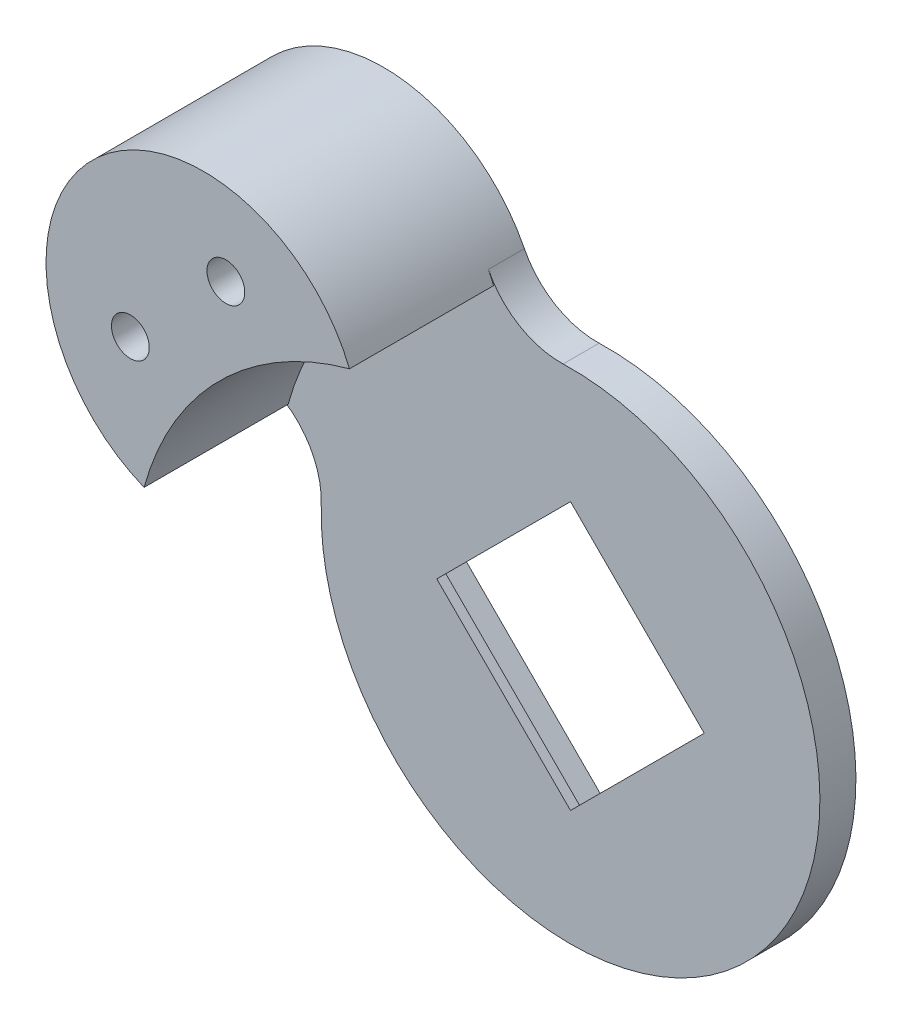
SolidWorks part; units mm, degrees
ref_plane "Front Plane" through (0, 0, 0) normal (0, 0, 1) x (1, 0, 0)
ref_plane "Top Plane" through (0, 0, 0) normal (0, 1, 0) x (1, 0, 0)
ref_plane "Right Plane" through (0, 0, 0) normal (1, 0, 0) x (0, 0, -1)
sketch "Sketch1" plane through (0, 0, 0) normal (0, 0, 1) x (1, 0, 0)
  arc A0 (-15.8844, 7.1509) -> (-38.6968, -15.6616) centre (-32.0888, 0.5429) ccw
  arc A2 (-19.7145, 12.9172) -> (-47.5228, -7.706) centre (-32.0888, 0.5429) ccw construction
  arc A3 (-15.8844, 7.1509) -> (-38.6968, -15.6616) centre (-7.3401, -24.2059) ccw
  dimension "D1" = 65
extrude "Boss-Extrude1" add sketch "Sketch1" along normal blind 16
sketch "Sketch2" plane through (0, 0, 0) normal (0, 0, -1) x (-1, 0, 0)
  circle A0 centre (7.3401, -24.2059) radius 27.6962 construction
  circle A1 centre (7.3401, -24.2059) radius 27.6962
  arc A2 (8.1602, 3.4781) -> (35.0241, -23.3857) centre (7.3401, -24.2059) ccw
  arc A3 (35.0241, -23.3857) -> (39.968, -15.083) centre (44.0202, -23.1192) cw
  arc A4 (38.6968, -15.6616) -> (15.8844, 7.1509) centre (7.3401, -24.2059) ccw
  arc A5 (38.6968, -15.6616) -> (15.8844, 7.1509) centre (32.0888, 0.5429) ccw
  arc A7 (39.968, -15.083) -> (16.4629, 8.4221) centre (32.0888, 0.5429) ccw
  arc A8 (8.1602, 3.4781) -> (16.4629, 8.4221) centre (8.4268, 12.4742) ccw
  point P0 (-30.618, 24.4257)
  point P13 (34.041, -16.8479)
  dimension "D3" = 9
  dimension "D1" = 0
  dimension "D2" = 0
extrude "Boss-Extrude2" add sketch "Sketch2" along normal blind 4
sketch "Sketch3" plane through (0, 0, -4) normal (0, 0, -1) x (-1, 0, 0)
  line L0 (40.2206, -1.932) -> (29.614, 8.6746) construction
  line L1 (7.3401, -24.2059) -> (34.9173, 3.3713) construction
  circle A0 centre (40.2206, -1.932) radius 2.1
  circle A1 centre (29.614, 8.6746) radius 2.1
  arc A2 (39.968, -15.083) -> (16.4629, 8.4221) centre (32.0888, 0.5429) ccw construction
  point P4 (44.4632, 12.9172)
  point P5 (-28.1337, 43.4891)
  dimension "D1" = 4.2
  dimension "D2" = 15
  dimension "D3" = 4
extrude "Cut-Extrude1" cut sketch "Sketch3" against normal through all
sketch "Sketch4" plane through (0, 0, -4) normal (0, 0, -1) x (-1, 0, 0)
  circle A0 centre (40.2206, -1.932) radius 4
  circle A1 centre (29.614, 8.6746) radius 4
  point P6 (-37.8732, 47.1192)
  point P7 (0, 0)
  point P8 (0, 0)
  dimension "D1" = 8
extrude "Cut-Extrude2" cut sketch "Sketch4" against normal offset from surface (14 mm away) 6 up to face at (-42.3206, -1.932, 16)
sketch "Sketch5" plane through (0, 0, -4) normal (0, 0, -1) x (-1, 0, 0)
  line L0 (23.6035, -24.2059) -> (7.3401, -7.9424)
  line L1 (23.6035, -24.2059) -> (7.3401, -40.4693)
  line L2 (7.3401, -7.9424) -> (-8.9234, -24.2059)
  line L3 (7.3401, -40.4693) -> (-8.9234, -24.2059)
  line L4 (23.6035, -24.2059) -> (-8.9234, -24.2059) construction
  line L5 (7.3401, -7.9424) -> (7.3401, -40.4693) construction
  line L6 (29.614, 8.6746) -> (40.2206, -1.932) construction
  arc A0 (8.1602, 3.4781) -> (35.0241, -23.3857) centre (7.3401, -24.2059) ccw construction
  point P1 (7.3401, -24.2059)
  point P12 (0, 0)
  dimension "D1" = 23
extrude "Cut-Extrude3" cut sketch "Sketch5" against normal offset from surface (3 mm away) 1 up to face at (-20.4825, -11.0635, 0)
sketch "Sketch6" plane through (0, 0, -1) normal (0, 0, -1) x (-1, 0, 0)
  line L8 (7.3401, -39.0551) -> (22.1893, -24.2059)
  line L9 (22.1893, -24.2059) -> (7.3401, -9.3566)
  line L10 (7.3401, -9.3566) -> (-7.5091, -24.2059)
  line L11 (-7.5091, -24.2059) -> (7.3401, -39.0551)
  line L12 (7.3401, -39.0551) -> (22.1893, -24.2059)
  line L13 (22.1893, -24.2059) -> (7.3401, -9.3566)
  line L14 (7.3401, -9.3566) -> (-7.5091, -24.2059)
  line L15 (-7.5091, -24.2059) -> (7.3401, -39.0551)
  dimension "D1" = 1
extrude "Cut-Extrude4" cut sketch "Sketch6" against normal through all
